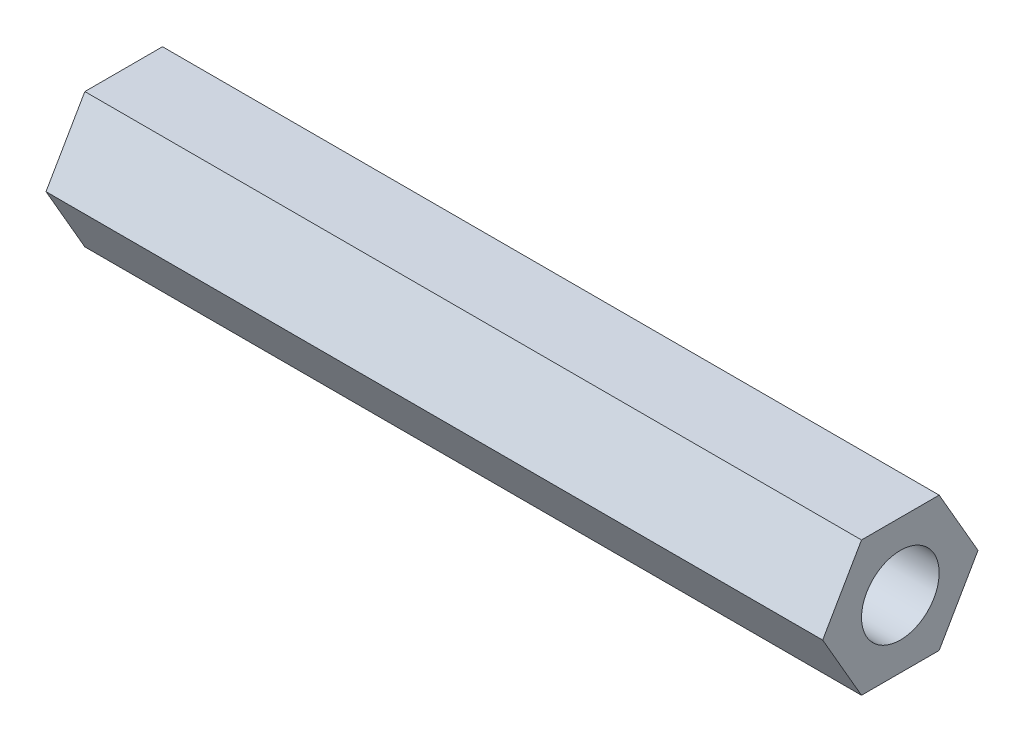
SolidWorks part; units mm, degrees
ref_plane "Front Plane" through (0, 0, 0) normal (0, 0, 1) x (1, 0, 0)
ref_plane "Top Plane" through (0, 0, 0) normal (0, 1, 0) x (1, 0, 0)
ref_plane "Right Plane" through (0, 0, 0) normal (1, 0, 0) x (0, 0, -1)
sketch "Sketch1" plane through (0, 0, 0) normal (1, 0, 0) x (0, 0, -1)
  line L1 (6.35, 0) -> (3.175, 5.4993)
  line L2 (3.175, 5.4993) -> (-3.175, 5.4993)
  line L3 (-3.175, 5.4993) -> (-6.35, 0)
  line L4 (-6.35, 0) -> (-3.175, -5.4993)
  line L5 (-3.175, -5.4993) -> (3.175, -5.4993)
  line L6 (3.175, -5.4993) -> (6.35, 0)
  circle A0 centre (0, 0) radius 5.4993 construction
  dimension "D1" = 6.35
extrude "Boss-Extrude1" add sketch "Sketch1" along normal blind 63.5
sketch "Sketch2" plane through (0, 0, 0) normal (-1, 0, 0) x (0, 0, 1)
  circle A0 centre (0, 0) radius 3.175
  dimension "D1" = 6.35
extrude "Cut-Extrude1" cut sketch "Sketch2" against normal through all
